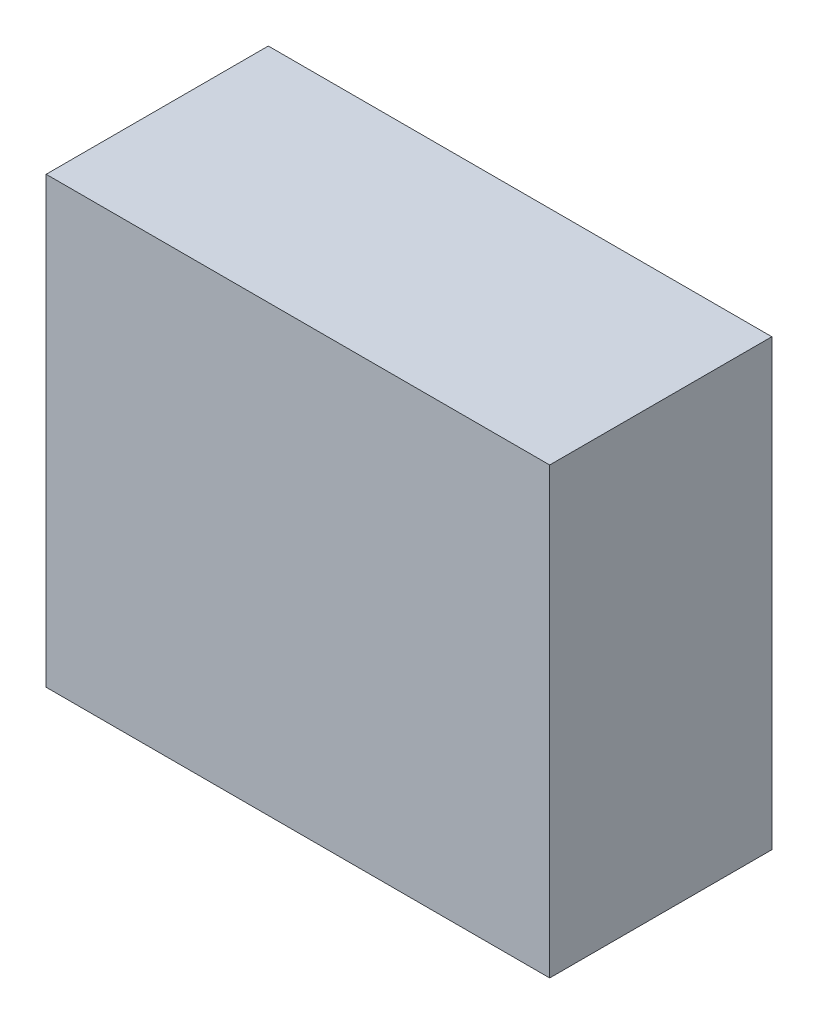
SolidWorks part; units mm, degrees
ref_plane "Front Plane" through (0, 0, 0) normal (0, 0, 1) x (1, 0, 0)
ref_plane "Top Plane" through (0, 0, 0) normal (0, 1, 0) x (1, 0, 0)
ref_plane "Right Plane" through (0, 0, 0) normal (1, 0, 0) x (0, 0, -1)
sketch "Sketch1" plane through (0, 0, 0) normal (0, 0, 1) x (1, 0, 0)
  line L1 (-17, -15) -> (17, -15)
  line L2 (-17, -15) -> (-17, 15)
  line L3 (-17, 15) -> (17, 15)
  line L4 (17, -15) -> (17, 15)
extrude "Boss-Extrude1" add sketch "Sketch1" along normal blind 15
sketch "Sketch2" plane through (0, 0, 0) normal (0, 0, -1) x (-1, 0, 0)
  circle A0 centre (-12, 9) radius 2 construction
  circle A1 centre (-12, -9) radius 2 construction
  circle A2 centre (12, -9) radius 2 construction
  circle A3 centre (12, 9) radius 2 construction
  circle A4 centre (-12, 9) radius 2 construction
  circle A5 centre (-12, -9) radius 2 construction
  circle A6 centre (12, -9) radius 2 construction
  circle A7 centre (12, 9) radius 2 construction
  circle A8 centre (12, -9) radius 2.1
  circle A9 centre (12, 9) radius 2.1
  circle A10 centre (-12, 9) radius 2.1
  circle A11 centre (-12, -9) radius 2.1
  dimension "D1" = 0.1
extrude "Cut-Extrude1" cut sketch "Sketch2" against normal blind 6
chamfer "Chamfer1" distance 1 angle 45 4 edges at (9.9, -9, 0) (-14.1, -9, 0) (-14.1, 9, 0) (9.9, 9, 0)
